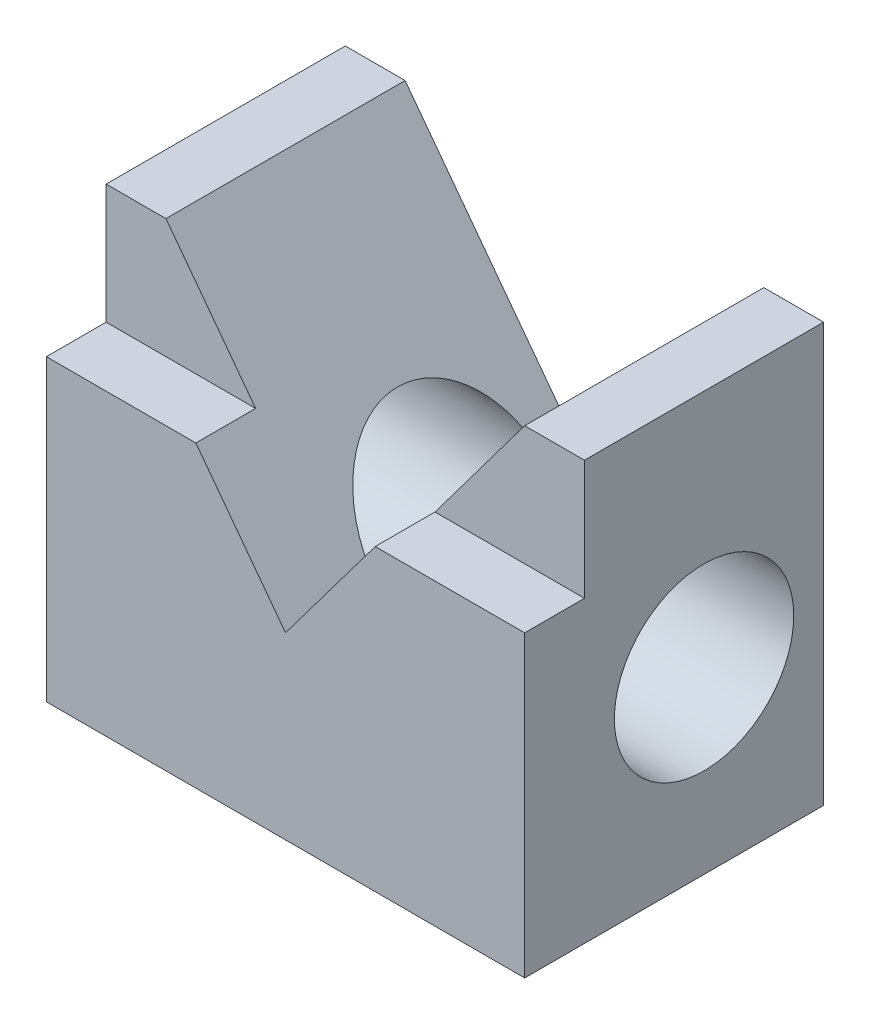
SolidWorks part; units mm, degrees
ref_plane "Front Plane" through (0, 0, 0) normal (0, 0, 1) x (1, 0, 0)
ref_plane "Top Plane" through (0, 0, 0) normal (0, 1, 0) x (1, 0, 0)
ref_plane "Right Plane" through (0, 0, 0) normal (1, 0, 0) x (0, 0, -1)
sketch "Sketch1" plane through (0, 0, 0) normal (0, 0, 1) x (1, 0, 0)
  line L0 (0, 0) -> (0, 88.9)
  line L1 (0, 88.9) -> (12.7, 88.9)
  line L2 (12.7, 88.9) -> (50.8, 38.1)
  line L3 (50.8, 38.1) -> (88.9, 88.9)
  line L4 (88.9, 88.9) -> (101.6, 88.9)
  line L5 (101.6, 88.9) -> (101.6, 0)
  line L6 (101.6, 0) -> (0, 0)
  dimension "D1" = 88.9
  dimension "D2" = 12.7
  dimension "D3" = 12.7
  dimension "D4" = 50.8
  dimension "D5" = 101.6
  dimension "D6" = 38.1
extrude "Boss-Extrude1" add sketch "Sketch1" along normal blind 63.5
sketch "Sketch2" plane through (0, 0, 0) normal (1, 0, 0) x (0, 0, -1)
  line L0 (0, 0) -> (0, 88.9) construction
  line L1 (-63.5, 0) -> (0, 0) construction
  circle A0 centre (-25.4, 38.1) radius 19.05
  dimension "D1" = 38.1
  dimension "D2" = 25.4
  dimension "D3" = 38.1
extrude "Cut-Extrude1" cut sketch "Sketch2" along normal through all
sketch "Sketch3" plane through (0, 0, 63.5) normal (0, 0, 1) x (1, 0, 0)
  line L0 (0, 63.5) -> (31.75, 63.5)
  line L1 (0, 88.9) -> (0, 0) construction
  line L2 (50.8, 38.1) -> (12.7, 88.9) construction
  line L3 (12.7, 88.9) -> (0, 88.9) construction
  line L4 (0, 63.5) -> (0, 88.9)
  line L5 (0, 88.9) -> (12.7, 88.9)
  line L6 (12.7, 88.9) -> (31.75, 63.5)
  line L7 (69.85, 63.5) -> (101.6, 63.5)
  line L10 (88.9, 88.9) -> (50.8, 38.1) construction
  line L12 (101.6, 63.5) -> (101.6, 88.9)
  line L13 (101.6, 88.9) -> (88.9, 88.9)
  line L14 (88.9, 88.9) -> (69.85, 63.5)
  dimension "D1" = 25.4
extrude "Cut-Extrude2" cut sketch "Sketch3" against normal blind 12.7
